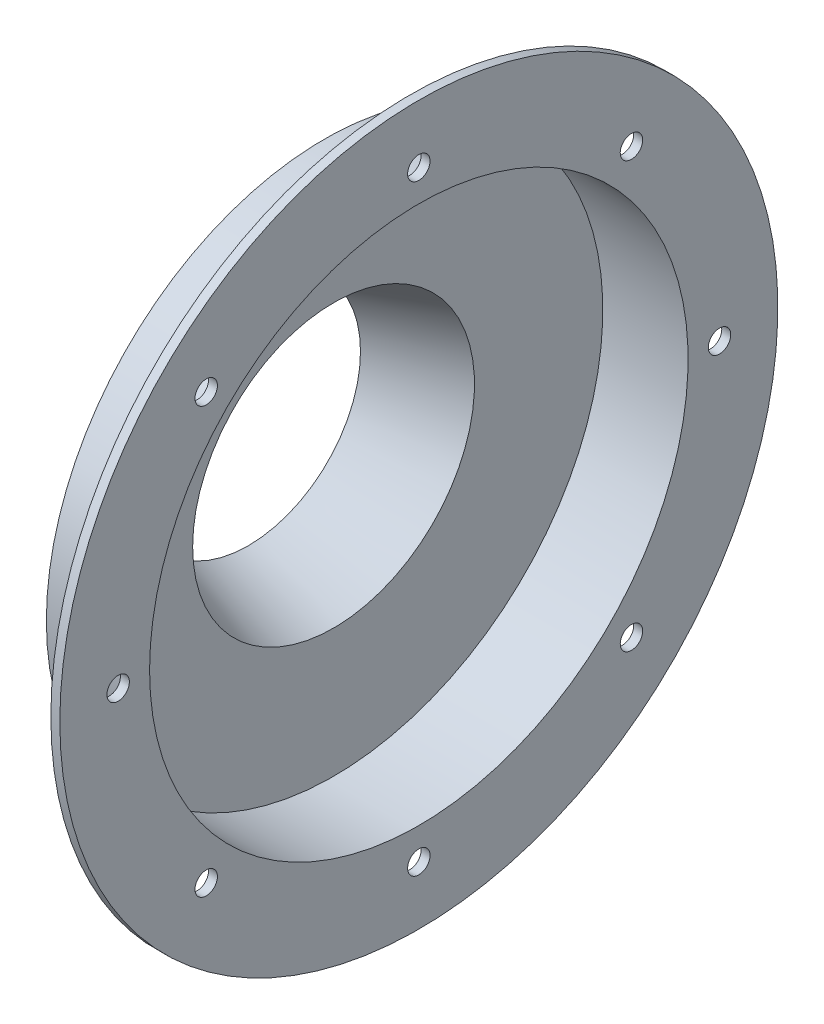
SolidWorks part; units mm, degrees
ref_plane "Front Plane" through (0, 0, 0) normal (0, 0, 1) x (1, 0, 0)
ref_plane "Top Plane" through (0, 0, 0) normal (0, 1, 0) x (1, 0, 0)
ref_plane "Right Plane" through (0, 0, 0) normal (1, 0, 0) x (0, 0, -1)
sketch "Sketch1" plane through (0, 0, 0) normal (0, 0, 1) x (1, 0, 0)
  line L0 (0, 0) -> (61.3012, 0) construction
  line L1 (0, 31.75) -> (24.13, 39.878)
  line L2 (24.13, 39.878) -> (24.13, 76.2)
  line L3 (24.13, 76.2) -> (48.26, 76.2)
  line L4 (48.26, 76.2) -> (48.26, 101.6)
  line L5 (-0.8108, 34.1571) -> (21.59, 41.7026)
  line L6 (21.59, 41.7026) -> (21.59, 78.74)
  line L7 (21.59, 78.74) -> (45.72, 78.74)
  line L8 (45.72, 78.74) -> (45.72, 101.6)
  line L9 (-0.8108, 34.1571) -> (0, 31.75)
  line L10 (45.72, 101.6) -> (48.26, 101.6)
  point P5 (30.6506, 0)
  dimension "D1" = 31.75
  dimension "D2" = 39.878
  dimension "D3" = 24.13
  dimension "D4" = 76.2
  dimension "D5" = 101.6
  dimension "D7" = 24.13
  dimension "D6" = 2.54
revolve "Revolve1" add sketch "Sketch1" angle 360 about L0
sketch "Sketch2" plane through (45.72, 0, 0) normal (-1, 0, 0) x (0, 0, 1)
  circle A0 centre (0, 85.09) radius 3.175
  dimension "D1" = 6.35
  dimension "D2" = 85.09
extrude "Cut-Extrude1" cut sketch "Sketch2" against normal blind 2.54
pattern_circular "CirPattern1" count 8 over 360 about axis through (0, 0, 0) along (1, 0, 0) of "Cut-Extrude1"
